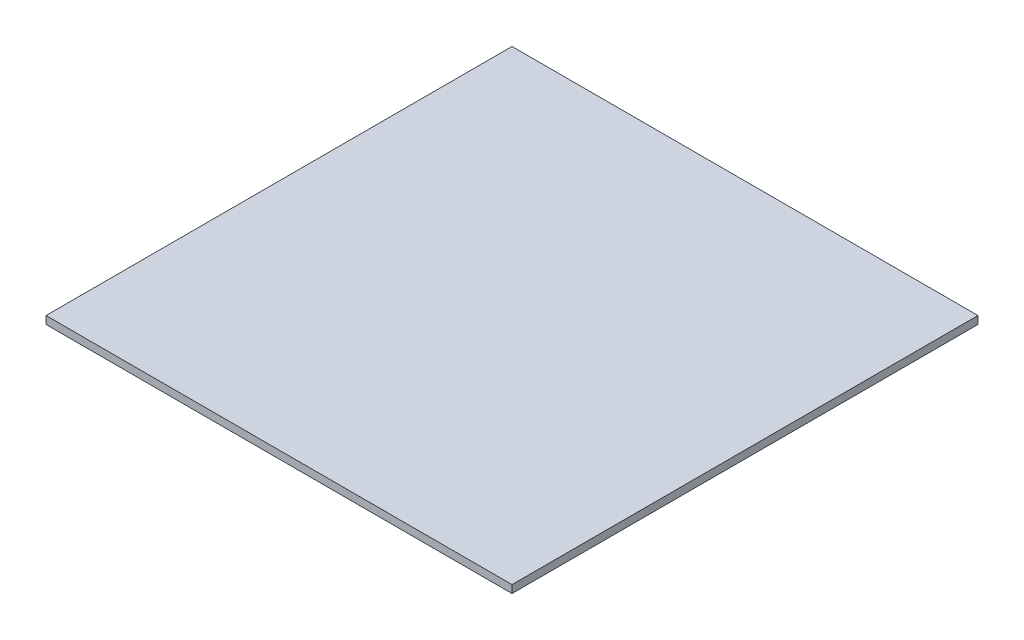
SolidWorks part; units mm, degrees
ref_plane "Front Plane" through (0, 0, 0) normal (0, 0, 1) x (1, 0, 0)
ref_plane "Top Plane" through (0, 0, 0) normal (0, 1, 0) x (1, 0, 0)
ref_plane "Right Plane" through (0, 0, 0) normal (1, 0, 0) x (0, 0, -1)
sketch "Sketch1" plane through (0, 0, 0) normal (0, 1, 0) x (1, 0, 0)
  line L1 (-762, 762) -> (762, 762)
  line L2 (-762, 762) -> (-762, -762)
  line L3 (-762, -762) -> (762, -762)
  line L4 (762, 762) -> (762, -762)
  line L5 (-762, 762) -> (762, -762) construction
  line L6 (-762, -762) -> (762, 762) construction
  point P0 (0, 0)
  dimension "D1" = 1524
  dimension "D2" = 1524
extrude "Boss-Extrude1" add sketch "Sketch1" along normal blind 25.4
